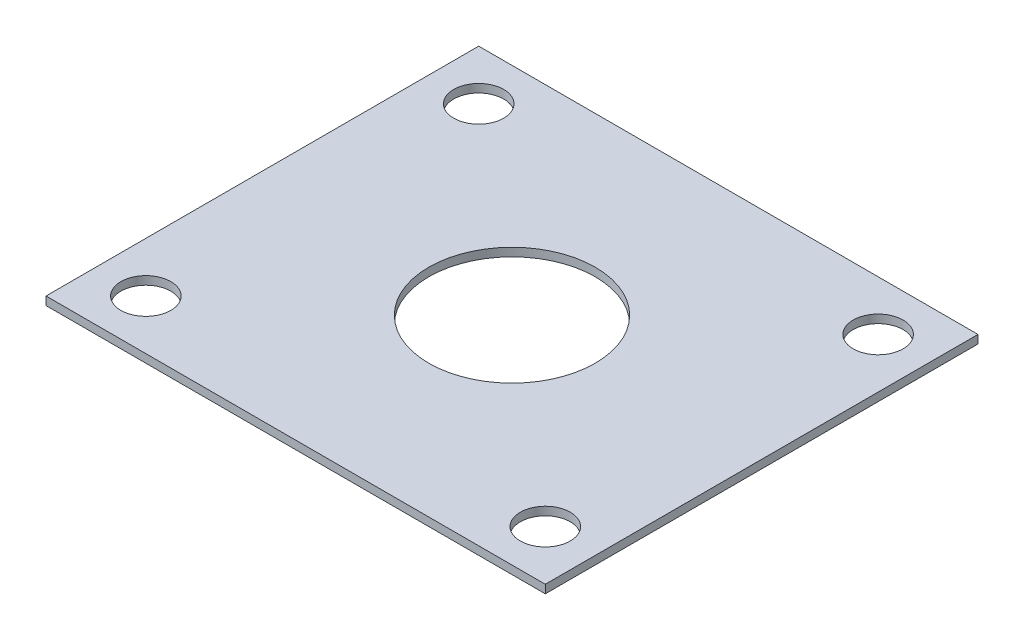
SolidWorks part; units mm, degrees
ref_plane "Front Plane" through (0, 0, 0) normal (0, 0, 1) x (1, 0, 0)
ref_plane "Top Plane" through (0, 0, 0) normal (0, 1, 0) x (1, 0, 0)
ref_plane "Right Plane" through (0, 0, 0) normal (1, 0, 0) x (0, 0, -1)
sketch "Sketch1" plane through (0, 0, 0) normal (0, 1, 0) x (1, 0, 0)
  line L1 (0, 0) -> (-38.1, 0)
  line L2 (0, 0) -> (0, 33.02)
  line L3 (0, 33.02) -> (-38.1, 33.02)
  line L4 (-38.1, 0) -> (-38.1, 33.02)
  dimension "D1" = 38.1
  dimension "D2" = 33.02
extrude "Boss-Extrude1" add sketch "Sketch1" along normal blind 0.635
sketch "Sketch2" plane through (0, 0.635, 0) normal (0, 1, 0) x (1, 0, 0)
  line L0 (-38.1, 0) -> (0, 0) construction
  line L1 (-38.1, 33.02) -> (-38.1, 0) construction
  circle A0 centre (-34.29, 29.21) radius 1.905
  circle A1 centre (-34.29, 3.81) radius 1.905
  circle A2 centre (-3.81, 29.21) radius 1.905
  circle A3 centre (-3.81, 3.81) radius 1.905
  dimension "D1" = 3.81
  dimension "D2" = 3.81
  dimension "D5" = 3.81
  dimension "D6" = 3.81
  dimension "D3" = 25.4
  dimension "D4" = 3.81
  dimension "D7" = 30.48
  dimension "D8" = 3.81
  dimension "D9" = 30.48
extrude "Cut-Extrude1" cut sketch "Sketch2" against normal blind 0.635
sketch "Sketch3" plane through (0, 0.635, 0) normal (0, 1, 0) x (1, 0, 0)
  line L1 (0, 33.02) -> (-38.1, 33.02) construction
  line L2 (-38.1, 33.02) -> (-38.1, 0) construction
  circle A0 centre (-19.05, 16.51) radius 6.35
  dimension "D1" = 12.7
  dimension "D2" = 16.51
  dimension "D3" = 19.05
extrude "Cut-Extrude2" cut sketch "Sketch3" against normal blind 0.635
